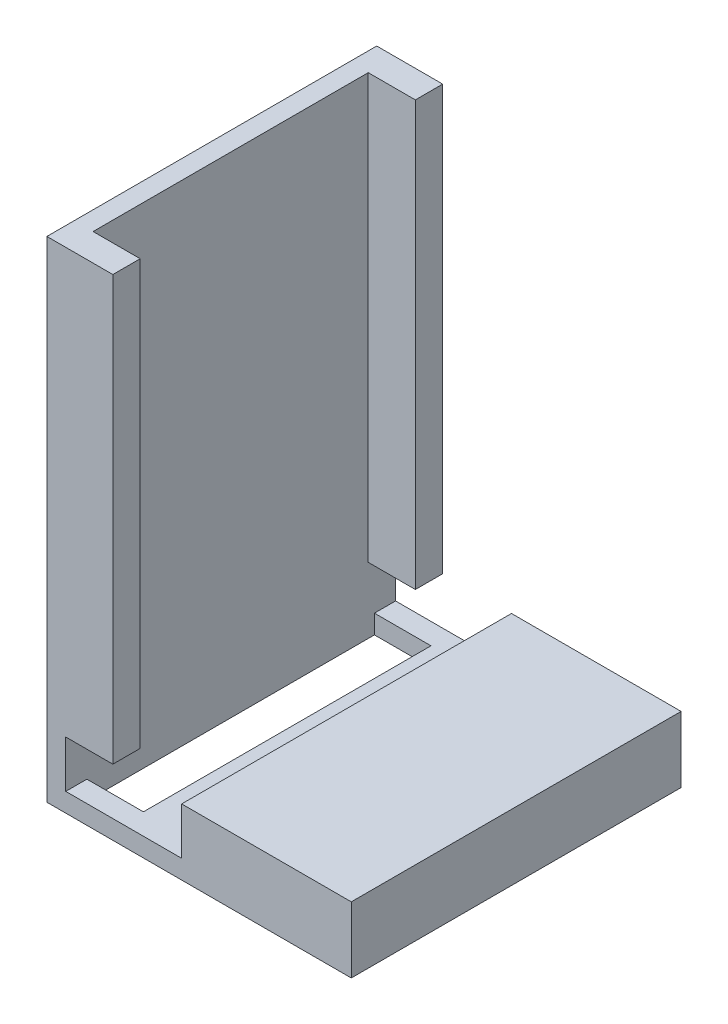
SolidWorks part; units mm, degrees
ref_plane "Front Plane" through (0, 0, 0) normal (0, 0, 1) x (1, 0, 0)
ref_plane "Top Plane" through (0, 0, 0) normal (0, 1, 0) x (1, 0, 0)
ref_plane "Right Plane" through (0, 0, 0) normal (1, 0, 0) x (0, 0, -1)
sketch "Sketch1" plane through (0, 0, 0) normal (0, 0, 1) x (1, 0, 0)
  line L1 (0, 0) -> (32.3, 0)
  line L2 (0, 0) -> (0, 2)
  line L3 (0, 2) -> (32.3, 2)
  line L4 (32.3, 0) -> (32.3, 2)
  line L5 (0, 0) -> (2, 0)
  line L6 (0, 0) -> (0, 52)
  line L7 (0, 52) -> (2, 52)
  line L8 (2, 0) -> (2, 52)
  line L9 (32.3, 2) -> (14.3, 2)
  line L10 (32.3, 2) -> (32.3, 7)
  line L11 (32.3, 7) -> (14.3, 7)
  line L12 (14.3, 2) -> (14.3, 7)
  dimension "D1" = 30.3
  dimension "D2" = 2
  dimension "D3" = 2
  dimension "D4" = 50
  dimension "D5" = 18
  dimension "D6" = 5
extrude "Boss-Extrude1" add sketch "Sketch1" along normal blind 35 contours L12 L3 L10 L11 | L8 L1 L4 L3 | L1 L8 L3 L2 | L3 L8 L7 L6
sketch "Sketch2" plane through (2, 0, 0) normal (1, 0, 0) x (0, 0, -1)
  line L0 (-35, 52) -> (0, 52) construction
  line L1 (-32.1, 52) -> (-2.9, 52)
  line L2 (-32.1, 52) -> (-32.1, 7)
  line L3 (-32.1, 7) -> (-2.9, 7)
  line L4 (-2.9, 52) -> (-2.9, 7)
  line L5 (-32.1, 52) -> (-2.9, 7) construction
  line L6 (-32.1, 7) -> (-2.9, 52) construction
  line L7 (-35, 7) -> (0, 7) construction
  line L9 (-35, 52) -> (0, 52)
  line L10 (-35, 52) -> (-35, 7)
  line L11 (-35, 7) -> (0, 7)
  line L12 (0, 52) -> (0, 7)
  point P0 (-17.5, 29.5)
  point P8 (-17.5, 52)
  line M5 (0, 2) -> (0, 52)
  line M6 (0, 52) -> (-35, 52)
  line M7 (-35, 52) -> (-35, 2)
  dimension "D1" = 29.2
extrude "Boss-Extrude2" add sketch "Sketch2" along normal blind 5 contours L11 L2 M7 M6 | L4 L11 M5 M6
sketch "Sketch3" plane through (0, 0, 0) normal (0, -1, 0) x (1, 0, 0)
  line L1 (2, 32.7572) -> (8, 32.7572)
  line L2 (2, 32.7572) -> (2, 2.2428)
  line L3 (2, 2.2428) -> (8, 2.2428)
  line L4 (8, 32.7572) -> (8, 2.2428)
  line L5 (0, 35) -> (0, 0) construction
  point P6 (0, 17.5)
  point P7 (2, 17.5)
  dimension "D1" = 6
  dimension "D2" = 2
extrude "Cut-Extrude1" cut sketch "Sketch3" against normal blind 5
